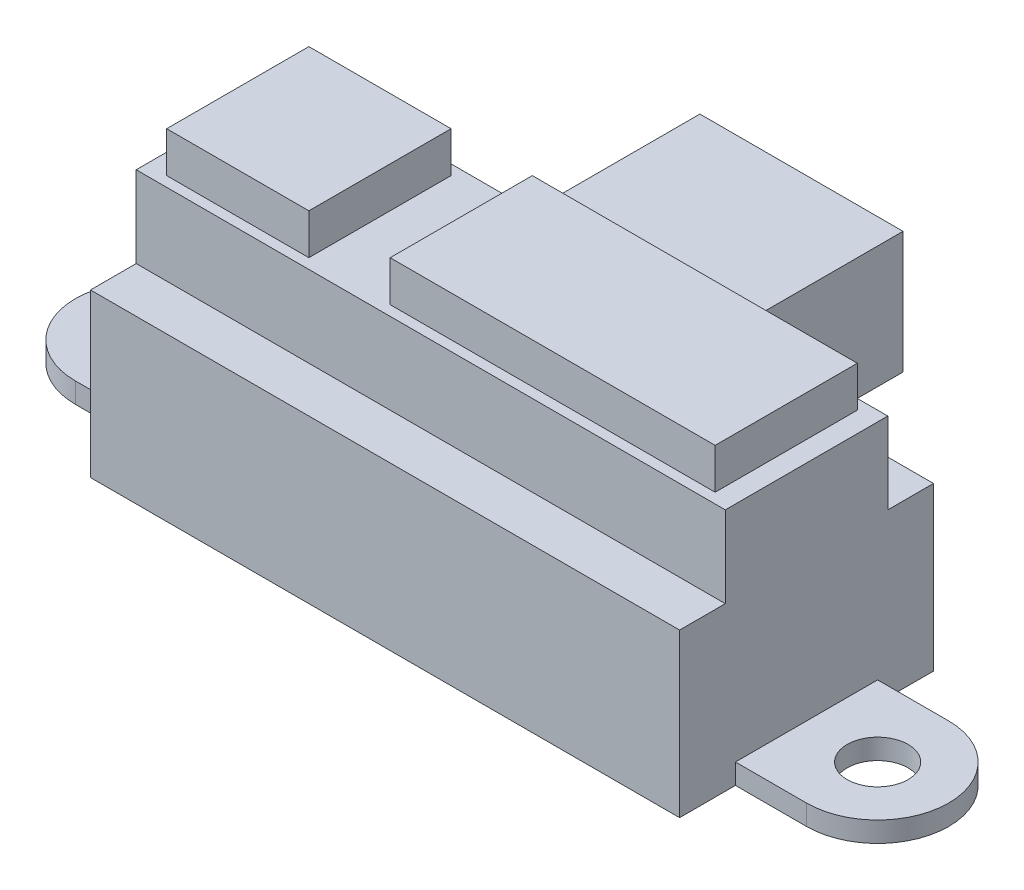
SolidWorks part; units mm, degrees
ref_plane "前视基准面" through (0, 0, 0) normal (0, 0, 1) x (1, 0, 0)
ref_plane "上视基准面" through (0, 0, 0) normal (0, 1, 0) x (1, 0, 0)
ref_plane "右视基准面" through (0, 0, 0) normal (1, 0, 0) x (0, 0, -1)
sketch "草图1" plane through (0, 0, 0) normal (0, 1, 0) x (1, 0, 0)
  line L0 (0, 0) -> (0, 5.0419) construction
  line L1 (0, 0) -> (-3.0581, 0) construction
  line L2 (-18, -3.5) -> (18, -3.5)
  line L3 (-18, 3.5) -> (18, 3.5)
  circle A0 centre (-18, 0) radius 1.5
  arc A2 (-18, 3.5) -> (-18, -3.5) centre (-18, 0) ccw
  arc A3 (18, 3.5) -> (18, -3.5) centre (18, 0) cw
  circle A4 centre (18, 0) radius 1.5
  dimension "D1" = 3
  dimension "D3" = 7
extrude "凸台-拉伸1" add sketch "草图1" along normal blind 1
sketch "草图3" plane through (0, 0, 0) normal (0, -1, 0) x (1, 0, 0)
  line L1 (14.5, -6.25) -> (-14.5, -6.25)
  line L2 (14.5, -6.25) -> (14.5, 6.25)
  line L3 (14.5, 6.25) -> (-14.5, 6.25)
  line L4 (-14.5, -6.25) -> (-14.5, 6.25)
  line L5 (14.5, -6.25) -> (-14.5, 6.25) construction
  line L6 (14.5, 6.25) -> (-14.5, -6.25) construction
  point P0 (0, 0)
  dimension "D1" = 29
  dimension "D2" = 12.5
extrude "凸台-拉伸2" add sketch "草图3" against normal blind 14
sketch "草图4" plane through (0, 0, -6.25) normal (0, 0, -1) x (-1, 0, 0)
  line L0 (0, 0) -> (0, 21.2853) construction
  line L1 (14.5, 0) -> (-14.5, 0) construction
  line L2 (-5, 4) -> (5, 4)
  line L3 (-5, 4) -> (-5, 10)
  line L4 (-5, 10) -> (5, 10)
  line L5 (5, 4) -> (5, 10)
  line L6 (-5, 4) -> (5, 10) construction
  line L7 (-5, 10) -> (5, 4) construction
  point P3 (0, 7)
  dimension "D1" = 10
  dimension "D2" = 6
  dimension "D3" = 4
extrude "凸台-拉伸3" add sketch "草图4" along normal blind 8
sketch "草图5" plane through (0, 14, 0) normal (0, 1, 0) x (1, 0, 0)
  line L1 (-14.5, -4) -> (14.5, -4)
  line L2 (-14.5, -4) -> (-14.5, 4)
  line L3 (-14.5, 4) -> (14.5, 4)
  line L4 (14.5, -4) -> (14.5, 4)
  line L5 (-14.5, -4) -> (14.5, 4) construction
  line L6 (-14.5, 4) -> (14.5, -4) construction
  line L7 (-14.5, -6.25) -> (14.5, -6.25)
  line L8 (-14.5, -6.25) -> (-14.5, 6.25)
  line L9 (-14.5, 6.25) -> (14.5, 6.25)
  line L10 (14.5, -6.25) -> (14.5, 6.25)
  line L11 (-14.5, -6.25) -> (14.5, 6.25) construction
  line L12 (-14.5, 6.25) -> (14.5, -6.25) construction
  point P0 (0, 0)
  point P6 (0, 0)
  line M5 (-14.5, 6.25) -> (-14.5, -6.25)
  line M6 (-14.5, -6.25) -> (14.5, -6.25)
  line M7 (14.5, -6.25) -> (14.5, 6.25)
  line M8 (14.5, 6.25) -> (-14.5, 6.25)
  dimension "D1" = 8
  dimension "D2" = 29
extrude "切除-拉伸1" cut sketch "草图5" against normal blind 6 contours L3 M5 M7 M8 | L1 M5 M6 M7
sketch "草图6" plane through (0, 14, 0) normal (0, 1, 0) x (1, 0, 0)
  line L0 (0, 0) -> (4.3823, 0) construction
  line L2 (-13.5, -3.5) -> (13.5, -3.5)
  line L3 (-13.5, -3.5) -> (-13.5, 3.5)
  line L4 (-13.5, 3.5) -> (13.5, 3.5)
  line L5 (13.5, -3.5) -> (13.5, 3.5)
  line L6 (-13.5, -3.5) -> (13.5, 3.5) construction
  line L7 (-13.5, 3.5) -> (13.5, -3.5) construction
  line L8 (-14.5, -6.25) -> (14.5, -6.25)
  line L9 (-14.5, -6.25) -> (-14.5, 6.25)
  line L10 (-14.5, 6.25) -> (14.5, 6.25)
  line L11 (14.5, -6.25) -> (14.5, 6.25)
  line L12 (-14.5, -6.25) -> (14.5, 6.25) construction
  line L13 (-14.5, 6.25) -> (14.5, -6.25) construction
  point P1 (0, 0)
  point P9 (0, 0)
  dimension "D1" = 7
  dimension "D2" = 27
extrude "切除-拉伸2" cut sketch "草图6" against normal blind 2
sketch "草图7" plane through (0, 14, 0) normal (0, 1, 0) x (1, 0, 0)
  line L0 (-13.5, 3.5) -> (-13.5, -3.5) construction
  line L1 (-6.5, 3.5) -> (-2.5, 3.5)
  line L2 (-6.5, 3.5) -> (-6.5, -3.5)
  line L3 (-6.5, -3.5) -> (-2.5, -3.5)
  line L4 (-2.5, 3.5) -> (-2.5, -3.5)
  dimension "D1" = 7
  dimension "D2" = 4
  dimension "D3" = 7
  dimension "D4" = 3.5
extrude "切除-拉伸3" cut sketch "草图7" against normal up to surface (2 mm away) up to face at (0, 12, 0)
